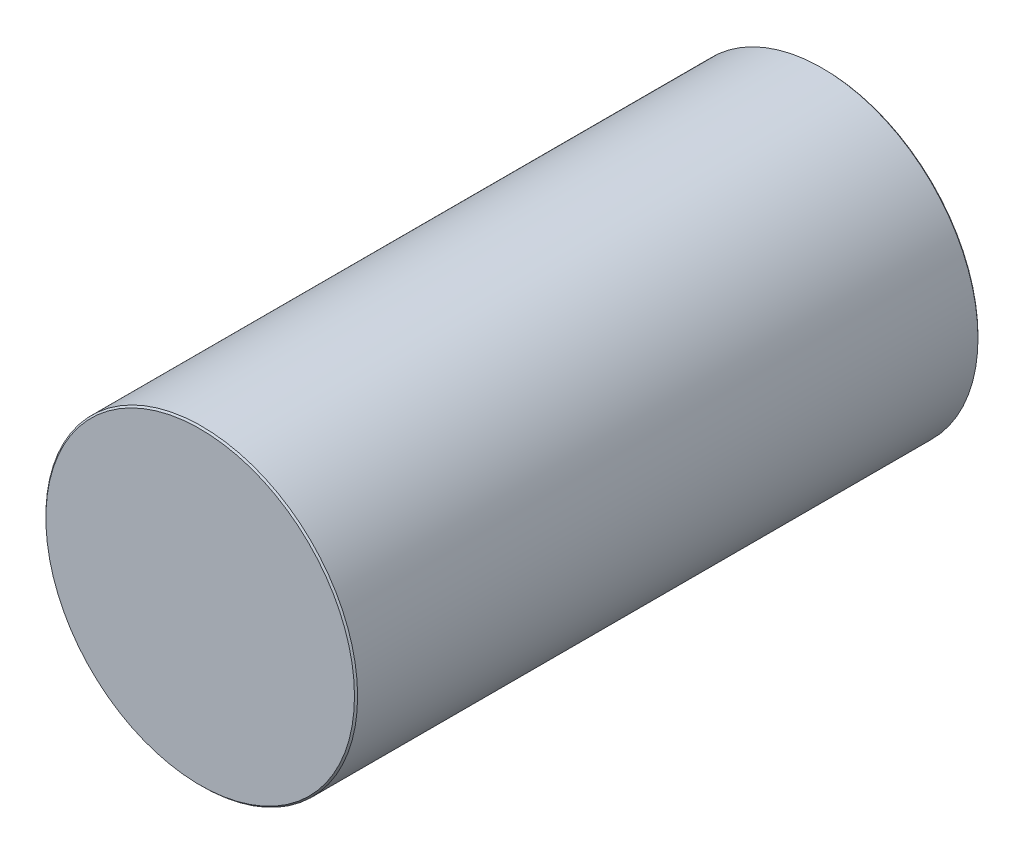
SolidWorks part; units mm, degrees
ref_plane "Front Plane" through (0, 0, 0) normal (0, 0, 1) x (1, 0, 0)
ref_plane "Top Plane" through (0, 0, 0) normal (0, 1, 0) x (1, 0, 0)
ref_plane "Right Plane" through (0, 0, 0) normal (1, 0, 0) x (0, 0, -1)
sketch "Sketch1" plane through (0, 0, 0) normal (0, 0, 1) x (1, 0, 0)
  circle A0 centre (0, 0) radius 100
  dimension "D1" = 200
extrude "Boss-Extrude1" add sketch "Sketch1" along normal blind 400
chamfer "Chamfer1" distance 1 angle 45 2 edges at (100, 0, 0) (100, 0, 400)
